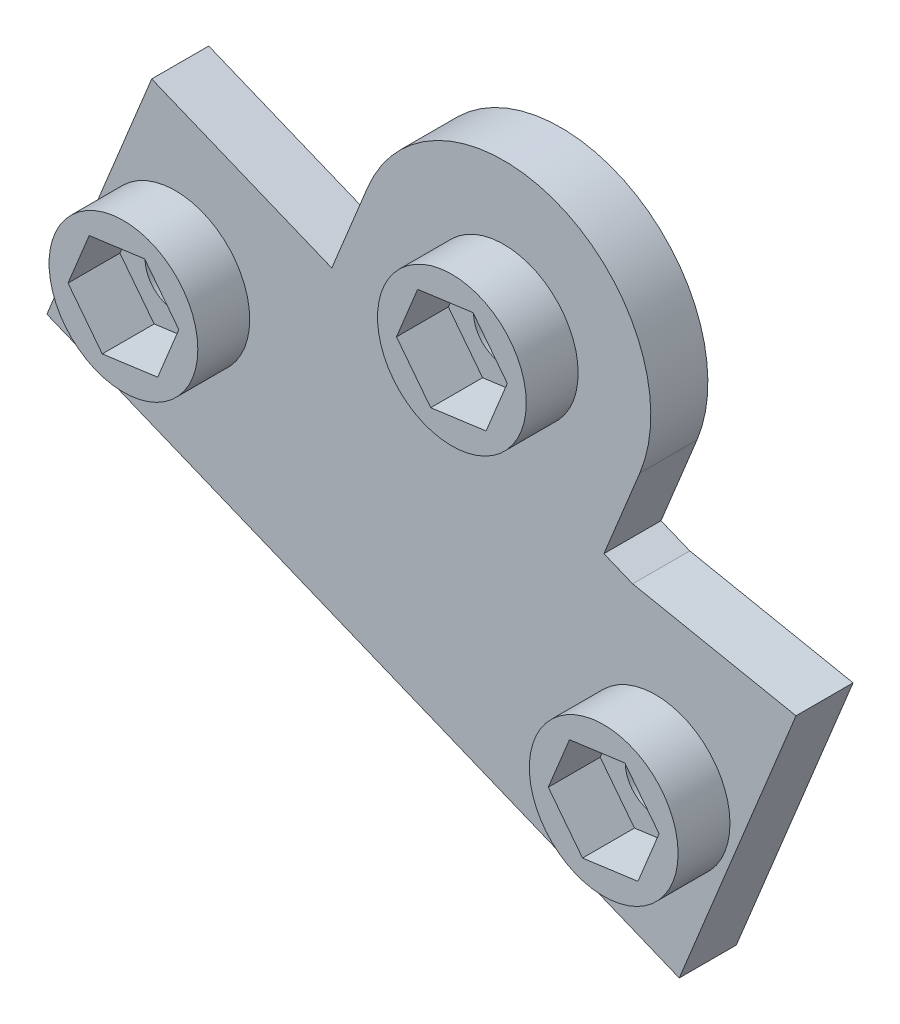
SolidWorks part; units mm, degrees
ref_plane "Front Plane" through (0, 0, 0) normal (0, 0, 1) x (1, 0, 0)
ref_plane "Top Plane" through (0, 0, 0) normal (0, 1, 0) x (1, 0, 0)
ref_plane "Right Plane" through (0, 0, 0) normal (1, 0, 0) x (0, 0, -1)
sketch "Sketch1" plane through (0, 0, 0) normal (0, 0, 1) x (1, 0, 0)
  line L0 (-67.8672, -11.1468) -> (-69.9439, -16.2233)
  line L1 (-52.1328, -17.5832) -> (-54.2095, -22.6598)
  line L2 (-86.4142, -26.7728) -> (-80.3564, -11.9639)
  line L3 (-49.8549, -41.7281) -> (-43.1038, -25.2247)
  line L6 (-68.0868, -16.983) -> (-80.5878, -11.8693)
  line L7 (-80.5878, -11.8693) -> (-86.6456, -26.6781)
  line L8 (-86.6456, -26.6781) -> (-49.6235, -41.8228)
  line L9 (-49.6235, -41.8228) -> (-42.8541, -25.2745)
  line L10 (-42.8541, -25.2745) -> (-52.5473, -23.3398)
  line L11 (-52.5473, -23.3398) -> (-56.0666, -21.9001)
  line L12 (-68.0868, -16.983) -> (-80.5878, -11.8693)
  line L13 (-80.5878, -11.8693) -> (-86.6456, -26.6781)
  line L14 (-86.6456, -26.6781) -> (-49.6235, -41.8228)
  line L15 (-49.6235, -41.8228) -> (-42.8541, -25.2745)
  line L16 (-42.8541, -25.2745) -> (-52.5473, -23.3398)
  line L17 (-52.5473, -23.3398) -> (-56.0666, -21.9001)
  circle A0 centre (-78.9889, -21.1668) radius 1.75 construction
  arc A1 (-68.0868, -16.983) -> (-56.0666, -21.9001) centre (-60, -14.365) ccw
  arc A2 (-68.0868, -16.983) -> (-56.0666, -21.9001) centre (-60, -14.365) ccw
  circle A3 centre (-51.2223, -32.5253) radius 1.75 construction
  circle A4 centre (-78.9889, -21.1668) radius 1.75
  circle A5 centre (-51.2223, -32.5253) radius 1.75
  circle A6 centre (-60, -14.365) radius 1.75
  circle A7 centre (-60, -14.365) radius 8.5
  dimension "D2" = 0.25
  dimension "D3" = 0.25
  dimension "D1" = 0
extrude "Boss-Extrude1" add sketch "Sketch1" along normal blind 3.3 contours A7 A2 A6 | A7 L0 L12 | A2 L12 L2 L14 L3 L16 L17 A5 A4 | A7 L17 L1
sketch "Sketch2" plane through (0, 0, 0) normal (0, 0, -1) x (-1, 0, 0)
  circle A0 centre (60, -14.365) radius 4.1
  circle A1 centre (60, -14.365) radius 1.75 construction
  circle A2 centre (60, -14.365) radius 1.75
  dimension "D1" = 8.2
extrude "Boss-Extrude2" [suppressed] add sketch "Sketch2" along normal blind 0.2
sketch "Sketch3" plane through (0, 0, 3.3) normal (0, 0, 1) x (1, 0, 0)
  line L0 (-86.4142, -26.7728) -> (-80.3564, -11.9639) construction
  line L1 (-77.7648, -18.1743) -> (-80.9684, -18.6104)
  line L2 (-80.9684, -18.6104) -> (-82.1925, -21.6029)
  line L3 (-82.1925, -21.6029) -> (-80.213, -24.1592)
  line L4 (-80.213, -24.1592) -> (-77.0094, -23.7231)
  line L5 (-77.0094, -23.7231) -> (-75.7853, -20.7307)
  line L6 (-75.7853, -20.7307) -> (-77.7648, -18.1743)
  line L7 (-49.8549, -41.7281) -> (-43.1038, -25.2247) construction
  line L8 (-52.4464, -35.5177) -> (-49.2428, -35.0816)
  line L9 (-49.2428, -35.0816) -> (-48.0187, -32.0892)
  line L10 (-48.0187, -32.0892) -> (-49.9982, -29.5328)
  line L11 (-49.9982, -29.5328) -> (-53.2018, -29.9689)
  line L12 (-53.2018, -29.9689) -> (-54.4259, -32.9614)
  line L13 (-54.4259, -32.9614) -> (-52.4464, -35.5177)
  line L14 (-67.8672, -11.1468) -> (-69.9439, -16.2233) construction
  line L15 (-61.2241, -17.3575) -> (-58.0205, -16.9214)
  line L16 (-58.0205, -16.9214) -> (-56.7964, -13.9289)
  line L17 (-56.7964, -13.9289) -> (-58.7759, -11.3725)
  line L18 (-58.7759, -11.3725) -> (-61.9795, -11.8086)
  line L19 (-61.9795, -11.8086) -> (-63.2036, -14.8011)
  line L20 (-63.2036, -14.8011) -> (-61.2241, -17.3575)
  circle A0 centre (-78.9889, -21.1668) radius 2.8 construction
  circle A1 centre (-51.2223, -32.5253) radius 2.8 construction
  circle A2 centre (-60, -14.365) radius 2.8 construction
  circle A3 centre (-78.9889, -21.1668) radius 4.3
  circle A4 centre (-60, -14.365) radius 4.3
  circle A5 centre (-51.2223, -32.5253) radius 4.3
  dimension "D2" = 8.6
  dimension "D1" = 5.6
extrude "Boss-Extrude3" add sketch "Sketch3" along normal blind 3 contours A3 L6 L5 L4 L3 L2 L1 | A4 L20 L19 L18 L17 L16 L15 | A5 L13 L12 L11 L10 L9 L8
